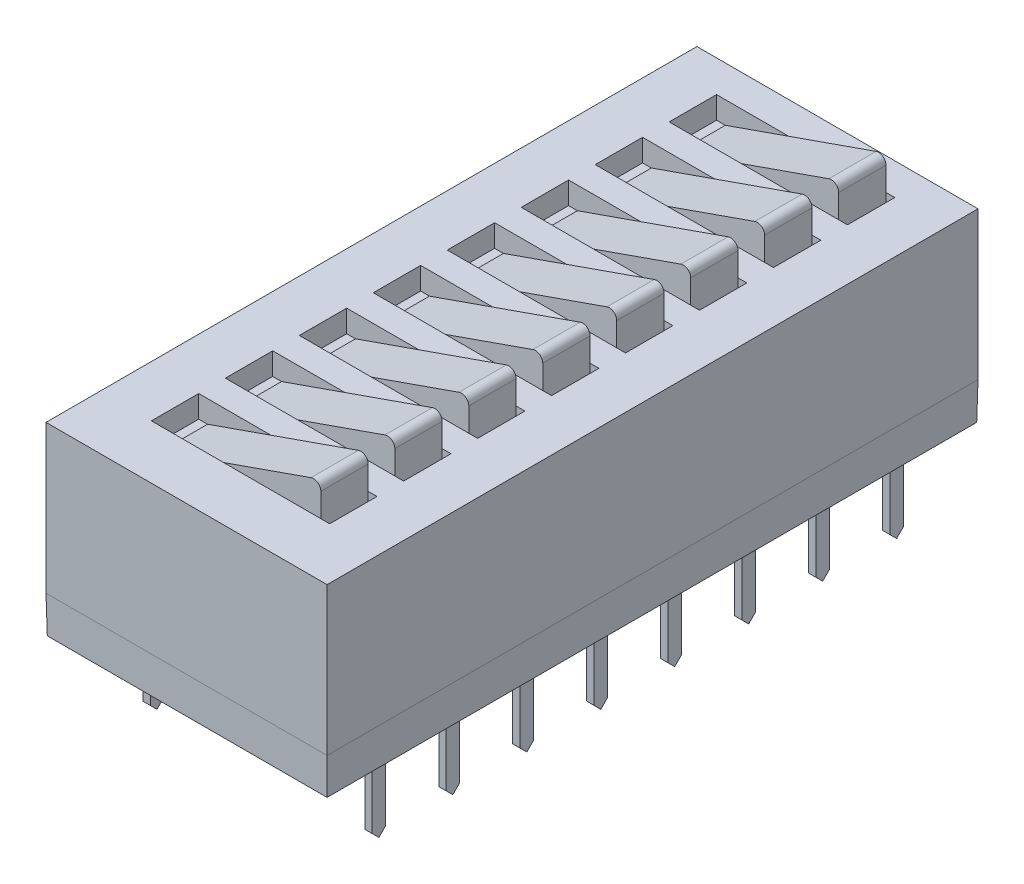
SolidWorks part; units mm, degrees
ref_plane "Front Plane" through (0, 0, 0) normal (0, 0, 1) x (1, 0, 0)
ref_plane "Top Plane" through (0, 0, 0) normal (0, 1, 0) x (1, 0, 0)
ref_plane "Right Plane" through (0, 0, 0) normal (1, 0, 0) x (0, 0, -1)
ref_plane "Plane1" through (0, 0.381, 0) normal (0, 1, 0) x (-1, 0, 0)
sketch "Sketch1" plane through (0, 0.381, 0) normal (0, 1, 0) x (0, 0, -1)
  line L1 (1.905, -8.636) -> (-20.447, -8.636)
  line L2 (1.905, -8.636) -> (1.905, 1.016)
  line L3 (1.905, 1.016) -> (-20.447, 1.016)
  line L4 (-20.447, -8.636) -> (-20.447, 1.016)
  dimension "D1" = 20.447
  dimension "D2" = 1.905
  dimension "D3" = 9.652
  dimension "D4" = 1.016
extrude "Base-Extrude" add sketch "Sketch1" along normal blind 6.35
chamfer "Chamfer1" distance 1.27 angle 1 4 edges at (8.636, 0.381, 9.271) (3.81, 0.381, 20.447) (-1.016, 0.381, 9.271) (3.81, 0.381, -1.905)
ref_plane "Plane2" through (8.636, 0, 0) normal (1, 0, 0) x (0, 0, -1)
ref_plane "Plane3" through (10.541, 0, 0) normal (1, 0, 0) x (0, 0, -1)
sketch "Sketch3" plane through (10.541, 0, 0) normal (0, 0, -1) x (-1, 0, 0)
  line L0 (10.541, 1.4986) -> (10.541, -2.5654)
  line L1 (10.033, 2.0066) -> (9.271, 2.0066)
  arc A0 (10.541, 1.4986) -> (10.033, 2.0066) centre (10.033, 1.4986) ccw
  dimension "D2" = 0.762
  dimension "D1" = 0.508
  dimension "D3" = 4.064
  dimension "D4" = 2.5654
extrude "Boss-Extrude-Thin1" add sketch "Sketch3" along normal mid plane 1.27 thin thin type mid plane wall 0.254
sketch "Sketch4" plane through (0.127, 0, 0) normal (1, 0, 0) x (0, 0, -1)
  line L0 (0.635, -2.5654) -> (-0.635, -2.5654) construction
  line L1 (0.635, -2.5654) -> (0.635, 0.381) construction
  line L2 (0.635, -2.5654) -> (0, -2.5654)
  line L3 (0.635, -2.5654) -> (0.635, 0.381)
  line L4 (0.635, 0.381) -> (0.2286, -0.0254)
  line L5 (0.2286, -0.0254) -> (0.2286, -2.3368)
  line L6 (0.2286, -2.3368) -> (0, -2.5654)
  dimension "D1" = 0.4064
  dimension "D2" = 45
extrude "Cut-Extrude1" cut sketch "Sketch4" against normal through all
sketch "Sketch5" plane through (0.127, 0, 0) normal (1, 0, 0) x (0, 0, -1)
  line L0 (-0.635, 0.381) -> (-0.2286, -0.0254)
  line L1 (-20.4248, 0.381) -> (1.8828, 0.381) construction
  line L2 (-0.2286, -0.0254) -> (-0.2286, -2.3368)
  line L3 (-0.2286, -2.3368) -> (0, -2.5654)
  line L4 (0.2286, -2.3368) -> (0, -2.5654) construction
  line L5 (0.635, 0.381) -> (0.2286, -0.0254) construction
  line L6 (-0.635, -2.5654) -> (-0.635, 0.381) construction
  line L7 (0, -2.5654) -> (-0.635, -2.5654) construction
  line L8 (-0.635, -2.5654) -> (-0.635, 0.381)
  line L9 (0, -2.5654) -> (-0.635, -2.5654)
extrude "Cut-Extrude2" cut sketch "Sketch5" against normal through all
pattern_linear "LPattern2" count 8 spacing 2.54 along (0, 0, 1) of "Cut-Extrude1", "Cut-Extrude2", "Boss-Extrude-Thin1"
ref_plane "Plane4" through (3.81, 0, 0) normal (-1, 0, 0) x (0, 0, 1)
mirror "Mirror1" about plane through (3.81, 0, 0) normal (-1, 0, 0) of "LPattern2", "Boss-Extrude-Thin1", "Cut-Extrude1", "Cut-Extrude2"
sketch "Sketch6" plane through (-4.3561, 6.731, -3.2639) normal (0, 1, 0) x (0, 0, -1)
  line L1 (-2.4511, -5.1054) -> (-4.0767, -5.1054)
  line L2 (-2.4511, -5.1054) -> (-2.4511, -11.2268)
  line L3 (-2.4511, -11.2268) -> (-4.0767, -11.2268)
  line L4 (-4.0767, -5.1054) -> (-4.0767, -11.2268)
  line L5 (-2.4511, -8.1661) -> (-1.3589, -8.1661) construction
  line L6 (-1.3589, -12.9921) -> (-1.3589, -3.3401) construction
  dimension "D1" = 6.1214
  dimension "D2" = 1.6256
  dimension "D3" = 1.0922
extrude "Cut-Extrude3" cut sketch "Sketch6" against normal blind 0.762
sketch "Sketch7" plane through (0, 0, -0.8128) normal (0, 0, 1) x (1, 0, 0)
  line L0 (1.052, 5.969) -> (6.2301, 7.7823)
  line L1 (6.568, 7.5426) -> (6.568, 5.969)
  line L2 (6.568, 5.969) -> (1.052, 5.969)
  line L3 (6.8707, 5.969) -> (0.7493, 5.969) construction
  arc A0 (6.568, 7.5426) -> (6.2301, 7.7823) centre (6.314, 7.5426) ccw
  point P7 (3.81, 5.969)
  dimension "D1" = 0.254
  dimension "D2" = 5.4864
  dimension "D3" = 19.3
extrude "Boss-Extrude1" add sketch "Sketch7" along normal blind 1.6256
pattern_linear "LPattern3" count 8 spacing 2.54 along (0, 0, 1) of "Boss-Extrude1", "Cut-Extrude3"
sketch "Component_Outline" plane through (0, 0, 0) normal (0, 1, 0) x (1, 0, 0)
  line L1 (-0.9938, -20.4248) -> (8.6138, -20.4248)
  line L2 (-0.9938, -20.4248) -> (-0.9938, 1.8828)
  line L3 (-0.9938, 1.8828) -> (8.6138, 1.8828)
  line L4 (8.6138, -20.4248) -> (8.6138, 1.8828)
